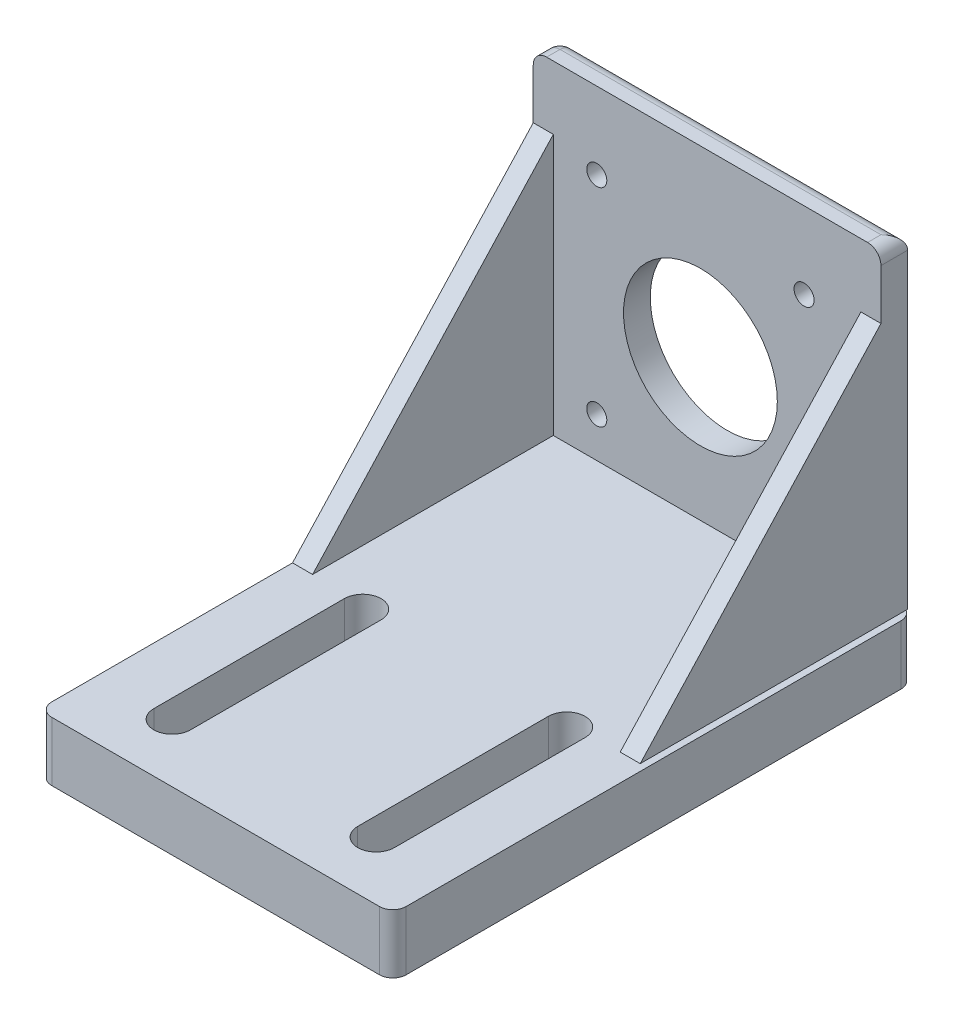
SolidWorks part; units mm, degrees
ref_plane "Front Plane" through (0, 0, 0) normal (0, 0, 1) x (1, 0, 0)
ref_plane "Top Plane" through (0, 0, 0) normal (0, 1, 0) x (1, 0, 0)
ref_plane "Right Plane" through (0, 0, 0) normal (1, 0, 0) x (0, 0, -1)
sketch "Sketch1" plane through (0, 0, 0) normal (0, 1, 0) x (1, 0, 0)
  line L0 (11, -54) -> (11, 24)
  line L1 (-42, -54) -> (11, -54)
  line L2 (-42, -54) -> (-42, 24)
  line L3 (-42, 24) -> (11, 24)
  dimension "D1" = 78
  dimension "D2" = 24
  dimension "D3" = 53
  dimension "D4" = 42
extrude "Boss-Extrude1" add sketch "Sketch1" along normal blind 8.85
fillet "Fillet2" radius 2 4 edges at (-42, 4.425, -24) (11, 4.425, -24) (11, 4.425, 54) (-42, 4.425, 54)
sketch "Sketch2" plane through (0, 8.85, 0) normal (0, 1, 0) x (1, 0, 0)
  line L0 (-42, 22) -> (-42, -52) construction
  line L5 (9, 24) -> (-40, 24) construction
  line L6 (-40, -54) -> (9, -54) construction
  line L8 (-33.5, -16.75) -> (-33.5, -45.25)
  line L10 (-28, -16.75) -> (-28, -45.25)
  line L11 (-15.5, 46.6682) -> (-15.5, -25.2267) construction
  line L12 (2.5, -16.75) -> (2.5, -45.25)
  line L13 (-3, -16.75) -> (-3, -45.25)
  arc A0 (2.5, -45.25) -> (-3, -45.25) centre (-0.25, -45.25) cw
  arc A1 (-33.5, -45.25) -> (-28, -45.25) centre (-30.75, -45.25) ccw
  arc A4 (-28, -16.75) -> (-33.5, -16.75) centre (-30.75, -16.75) ccw
  arc A5 (-3, -16.75) -> (2.5, -16.75) centre (-0.25, -16.75) cw
  dimension "D5" = 5.5
  dimension "D6" = 8.75
  dimension "D8" = 2.75
  dimension "D9" = 2.75
  dimension "D11" = 15.25
  dimension "D4" = 28.5
  dimension "D7" = 11.25
  dimension "D10" = 5.5
extrude "Cut-Extrude1" cut sketch "Sketch2" against normal through all and the other way through all
sketch "Sketch3" plane through (0, 8.85, 0) normal (0, 1, 0) x (1, 0, 0)
  line L0 (-42, 22) -> (-42, -52) construction
  line L1 (-42, 20) -> (10, 20)
  line L2 (-42, 20) -> (-42, 22)
  line L3 (-40, 24) -> (10, 24)
  line L4 (10, 20) -> (10, 24)
  line L5 (9, 24) -> (-40, 24) construction
  arc A2 (-40, 24) -> (-42, 22) centre (-40, 22) ccw
  arc A3 (-40, 24) -> (-42, 22) centre (-40, 22) ccw
  dimension "D1" = 50
  dimension "D2" = 4
  dimension "D3" = 0
extrude "Boss-Extrude2" add sketch "Sketch3" along normal blind 48.5
fillet "Fillet4" radius 2 4 edges at (-15, 57.35, -24) (-41.4142, 57.35, -23.4142) (10, 57.35, -22) (-42, 57.35, -21)
sketch "Sketch4" plane through (-42, 0, 0) normal (-1, 0, 0) x (0, 0, 1)
  line L0 (16, 8.85) -> (-20, 47.85)
  line L1 (-20, 8.85) -> (52, 8.85) construction
  line L2 (-20, 55.35) -> (-20, 8.85) construction
  dimension "D1" = 7.5
rib "Rib7" sketch "Sketch4" sketch "Sketch4" thickness 3 extrusion direction parallel to sketch draft on no parameters "D1"=3
sketch "Sketch6" plane through (10, 0, 0) normal (1, 0, 0) x (0, 0, -1)
  line L0 (20, 47.85) -> (-16, 8.85)
rib "Rib8" sketch "Sketch6" sketch "Sketch6" thickness 3 extrusion direction parallel to sketch draft on no parameters "D1"=3
sketch "Sketch7" plane through (0, 0, -20) normal (0, 0, 1) x (1, 0, 0)
  line L0 (-17, 58.1041) -> (-17, -5.9394) construction
  line L1 (-39, 8.85) -> (-39, 47.85) construction
  line L3 (-40, 57.35) -> (8, 57.35) construction
  circle A0 centre (-17, 30) radius 11.5
  circle A1 centre (-32.5, 45.85) radius 1.5
  circle A2 centre (-32.5, 14.85) radius 1.5
  circle A3 centre (-1.5, 14.85) radius 1.5
  circle A4 centre (-1.5, 45.85) radius 1.5
  dimension "D2" = 27.35
  dimension "D3" = 23
  dimension "D4" = 3
  dimension "D5" = 3
  dimension "D1" = 22
  dimension "D6" = 31
  dimension "D7" = 11.5
  dimension "D8" = 15.5
extrude "Cut-Extrude2" cut sketch "Sketch7" against normal through all
